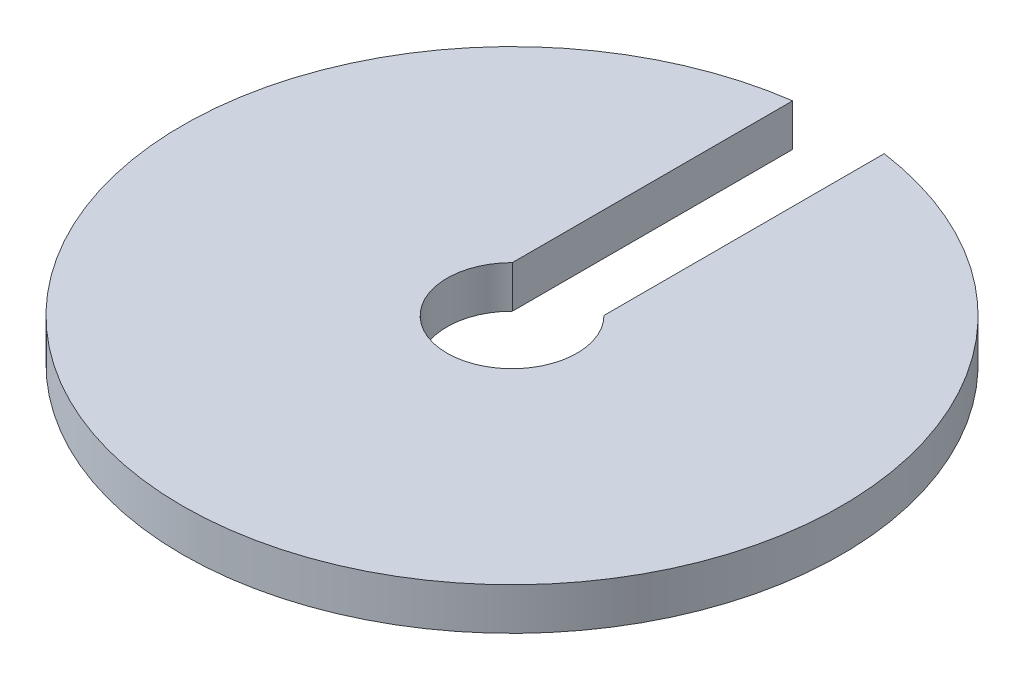
SolidWorks part; units mm, degrees
ref_plane "Alzado" through (0, 0, 0) normal (0, 0, 1) x (1, 0, 0)
ref_plane "Planta" through (0, 0, 0) normal (0, 1, 0) x (1, 0, 0)
ref_plane "Vista lateral" through (0, 0, 0) normal (1, 0, 0) x (0, 0, -1)
sketch "Croquis1" plane through (0, 0, 0) normal (0, 1, 0) x (1, 0, 0)
  line L0 (-2.5, 2.5204) -> (-2.5, 17.8255)
  line L1 (2.5, 17.8255) -> (2.5, 2.5204)
  arc A0 (-2.5, 17.8255) -> (2.5, 17.8255) centre (0, 0) ccw
  arc A1 (-2.5, 2.5204) -> (2.5, 2.5204) centre (0, 0) ccw
  dimension "D1" = 36
  dimension "D2" = 7.1
  dimension "D3" = 5
extrude "Saliente-Extruir1" add sketch "Croquis1" along normal blind 2.3
